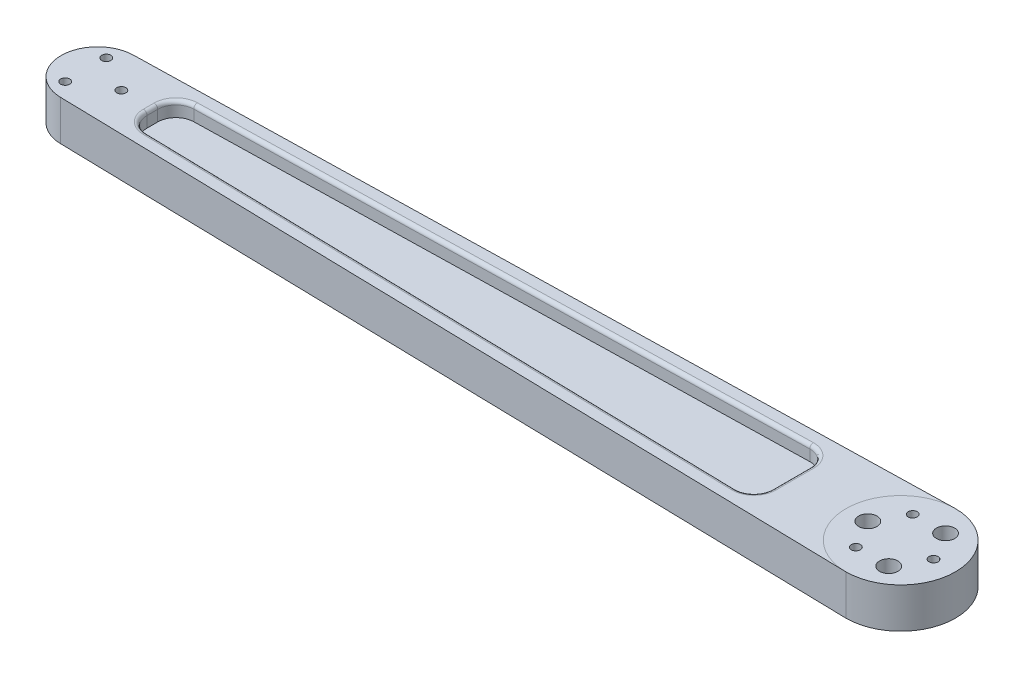
SolidWorks part; units mm, degrees
material "7075-T6, 플레이트 (SS)"
ref_plane "정면" through (0, 0, 0) normal (0, 0, 1) x (1, 0, 0)
ref_plane "윗면" through (0, 0, 0) normal (0, 1, 0) x (1, 0, 0)
ref_plane "우측면" through (0, 0, 0) normal (1, 0, 0) x (0, 0, -1)
sketch "스케치1" plane through (0, 0, 0) normal (0, 1, 0) x (1, 0, 0)
  line L0 (0, -15) -> (-220.2271, -9.998)
  line L1 (0, 0) -> (-220, 0) construction
  line L3 (0, 15) -> (-220.2271, 9.998)
  arc A1 (0, -15) -> (0, 15) centre (0, 0) ccw
  arc A3 (-220.2271, 9.998) -> (-220.2271, -9.998) centre (-220, 0) ccw
  dimension "D1" = 30
  dimension "D3" = 30
  dimension "D2" = 9.998
  dimension "D4" = 220
extrude "보스-돌출2" add sketch "스케치1" along normal blind 11
sketch "스케치5" plane through (0, 11, 0) normal (0, 1, 0) x (1, 0, 0)
  circle A0 centre (0, 0) radius 9 construction
  dimension "D1" = 18
hole_wizard "M3 탭을 위한 탭 드릴1" positions "스케치8" profile "스케치9" hole size "M3" standard "ISO" end condition through all
sketch "스케치8" plane through (0, 11, 0) normal (0, 1, 0) x (1, 0, 0)
  circle A0 centre (0, 0) radius 9 construction
  point P0 (9, 0)
sketch "스케치9" plane through (9, 11, 0) normal (1, 0, 0) x (0, 0, 1)
  line L0 (0, 0) -> (0, 11)
  line L1 (0, 11) -> (1.25, 11)
  line L2 (1.25, 11) -> (1.25, 0)
  line L5 (1.25, 0) -> (0, 0)
  line L11 (0, -6.35) -> (0, 107.95) construction
  dimension "관통 구멍 지름" = 2.5
  dimension "관통 구멍 깊이" = 11
pattern_circular "원형 패턴2" count 3 over 360 about axis through (0, 0, 0) along (0, 1, 0) of "M3 탭을 위한 탭 드릴1"
sketch "스케치10" plane through (0, 11, 0) normal (0, 1, 0) x (1, 0, 0)
  circle A0 centre (0, 0) radius 15
  dimension "D1" = 30
split line "분할선1"
ref_plane "평면1" through (0, 0, 0) normal (0, 0, 1) x (1, 0, 0)
sketch "스케치13" plane through (0, 0, 0) normal (0, -1, 0) x (1, 0, 0)
  circle A0 centre (0, 0) radius 15
  dimension "D1" = 30
split line "분할선2"
hole_wizard "Ø5.0mm 맞춤핀 구멍1" [suppressed] positions "스케치14" profile "스케치16" hole size "Ø5.0" standard "ISO"
sketch "스케치14" plane through (0, 11, 0) normal (0, 1, 0) x (1, 0, 0)
  circle A0 centre (0, 0) radius 9 construction
  point P0 (-9, 0)
sketch "스케치16" plane through (-9, 11, 0) normal (1, 0, 0) x (0, 0, 1)
  line L0 (0, 0) -> (0, 11.015)
  line L1 (0, 11.015) -> (2.5, 11.015)
  line L2 (2.5, 11.015) -> (2.5, 0)
  line L5 (2.5, 0) -> (0, 0)
  line L11 (0, -6.35) -> (0, 107.95) construction
  dimension "관통 구멍 지름" = 5
  dimension "관통 구멍 깊이" = 11.015
pattern_circular "원형 패턴3" [suppressed] count 3 over 360
sketch "스케치18" plane through (0, 11, 0) normal (0, 1, 0) x (1, 0, 0)
  circle A0 centre (-220, 0) radius 6.5
  point P3 (-213.5, 0)
  dimension "D1" = 13
hole_wizard "M3 탭을 위한 탭 드릴2" positions "스케치19" profile "스케치20" hole size "M3" standard "ISO" end condition through all
sketch "스케치19" plane through (0, 11, 0) normal (0, 1, 0) x (1, 0, 0)
  point P0 (-213.5, 0)
sketch "스케치20" plane through (-213.5, 11, 0) normal (1, 0, 0) x (0, 0, 1)
  line L0 (0, 0) -> (0, 11.0341)
  line L1 (0, 11.0341) -> (1.25, 11.0341)
  line L2 (1.25, 11.0341) -> (1.25, 0)
  line L5 (1.25, 0) -> (0, 0)
  line L11 (0, -6.35) -> (0, 107.95) construction
  dimension "관통 구멍 지름" = 2.5
  dimension "관통 구멍 깊이" = 11.0341
pattern_circular "원형 패턴4" count 3 over 360 about axis through (-220, 0, 0) along (0, 1, 0) of "M3 탭을 위한 탭 드릴2"
hole_wizard "Ø5.0mm 맞춤핀 구멍2" positions "스케치24" profile "스케치25" hole size "Ø5.0" standard "ISO" end condition through all
sketch "스케치24" plane through (0, 11, 0) normal (0, 1, 0) x (1, 0, 0)
  circle A0 centre (0, 0) radius 9 construction
  point P0 (-9, 0)
sketch "스케치25" plane through (-9, 11, 0) normal (1, 0, 0) x (0, 0, 1)
  line L0 (0, 0) -> (0, 11.0341)
  line L1 (0, 11.0341) -> (2.5, 11.0341)
  line L2 (2.5, 11.0341) -> (2.5, 0)
  line L5 (2.5, 0) -> (0, 0)
  line L11 (0, -6.35) -> (0, 107.95) construction
  dimension "관통 구멍 지름" = 5
  dimension "관통 구멍 깊이" = 11.0341
pattern_circular "원형 패턴5" count 3 over 360 about axis through (0, 0, 0) along (0, 1, 0) of "Ø5.0mm 맞춤핀 구멍2"
sketch "스케치26" plane through (0, 11, 0) normal (0, 1, 0) x (1, 0, 0)
  line L0 (-220.2271, -9.998) -> (-0.681, -14.9845) construction
  line L1 (-230.0006, 0) -> (21.9081, 0) construction
  line L2 (-0.5902, 10.9856) -> (-220.1363, 5.999)
  line L3 (-30, 10.3176) -> (-205, 6.3428)
  line L4 (-30, -10.3176) -> (-205, -6.3428)
  line L5 (-205, -6.3428) -> (-205, 6.3428)
  line L6 (-30, -10.3176) -> (-30, 10.3176)
  arc A0 (-220.2271, 9.998) -> (-220.2271, -9.998) centre (-220, 0) ccw construction
  dimension "D2" = 15
  dimension "D3" = 30
  dimension "D4" = 4
  dimension "D1" = 4
extrude "컷-돌출1" cut sketch "스케치26" against normal blind 4
fillet "필렛2" radius 5 4 edges at (-205, 9, 6.3428) (-205, 9, -6.3428) (-30, 9, 10.3176) (-30, 9, -10.3176)
ref_plane "평면3" through (0, 5.5, 0) normal (0, 1, 0) x (1, 0, 0)
mirror "대칭 복사4" about plane through (0, 5.5, 0) normal (0, 1, 0) of "컷-돌출1"
fillet "필렛4" radius 5 4 edges at (-205, 2, 6.3428) (-205, 2, -6.3428) (-30, 2, 10.3176) (-30, 2, -10.3176)
fillet "필렛5" radius 1 8 edges at (-203.5754, 0, -4.9503) (-203.5754, 0, 4.9503) (-205, 0, 0) (-117.6135, 0, 8.3276) (-117.6135, 0, -8.3276) (-31.5048, 0, -8.7782) (-31.5048, 0, 8.7782) (-30, 0, 0)
fillet "필렛6" radius 1 8 edges at (-31.5048, 11, -8.7782) (-30, 11, 0) (-31.5048, 11, 8.7782) (-117.6135, 11, -8.3276) (-117.6135, 11, 8.3276) (-203.5754, 11, 4.9503) (-203.5754, 11, -4.9503) (-205, 11, 0)
